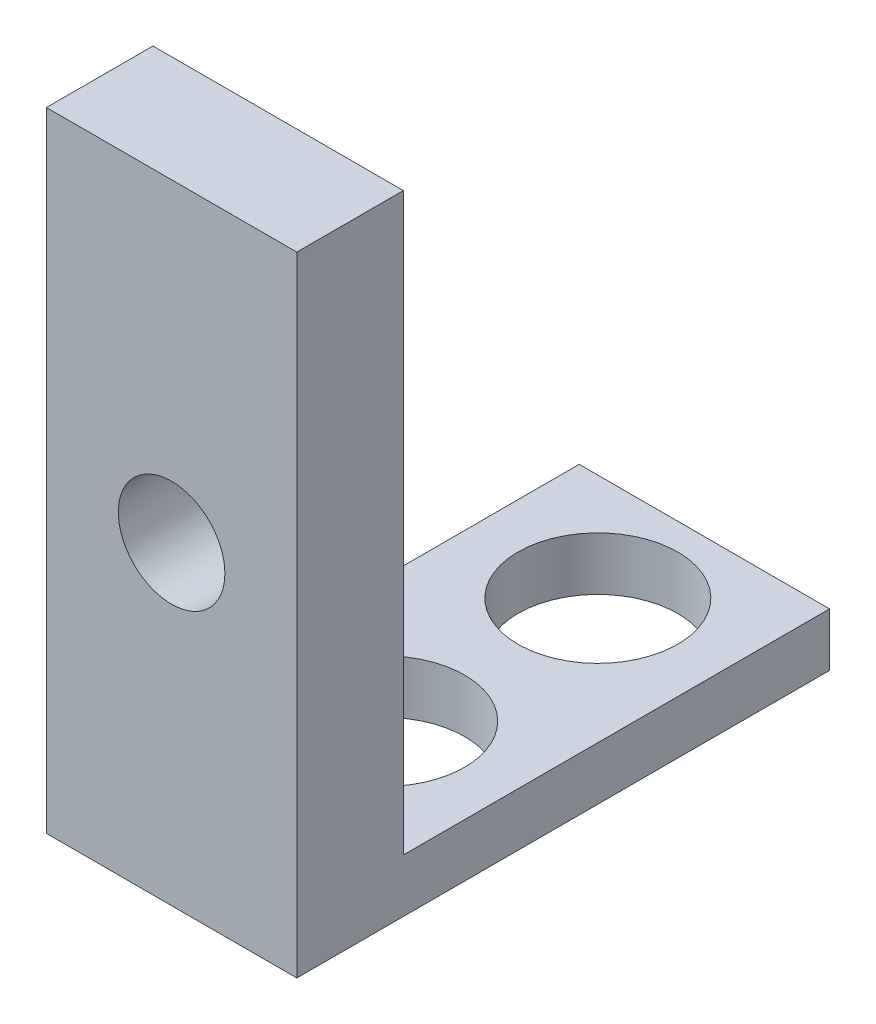
SolidWorks part; units mm, degrees
ref_plane "Front Plane" through (0, 0, 0) normal (0, 0, 1) x (1, 0, 0)
ref_plane "Top Plane" through (0, 0, 0) normal (0, 1, 0) x (1, 0, 0)
ref_plane "Right Plane" through (0, 0, 0) normal (1, 0, 0) x (0, 0, -1)
sketch "Sketch1" plane through (0, 0, 0) normal (0, 0, 1) x (1, 0, 0)
  line L0 (0, 0) -> (0, 11.8)
  line L1 (0, 0) -> (4.7, 0)
  line L2 (4.7, 0) -> (4.7, 11.8)
  line L3 (4.7, 11.8) -> (0, 11.8)
  circle A0 centre (2.35, 5.9) radius 1
  point P3 (2.35, 11.8)
  point P6 (2.35, 5.9)
  dimension "D3" = 2
  dimension "D1" = 11.8
  dimension "D2" = 4.7
extrude "Boss-Extrude1" add sketch "Sketch1" along normal blind 2
sketch "Sketch2" plane through (0, 0, 0) normal (0, 0, -1) x (-1, 0, 0)
  line L0 (0, 11.8) -> (0, 0) construction
  line L1 (-4.7, 0) -> (0, 0)
  line L2 (-4.7, 0) -> (-4.7, 1)
  line L3 (-4.7, 1) -> (0, 1)
  line L4 (0, 0) -> (0, 1)
  dimension "D1" = 1
extrude "Boss-Extrude2" add sketch "Sketch2" along normal blind 8
sketch "Sketch3" plane through (0, 1, 0) normal (0, 1, 0) x (1, 0, 0)
  line L0 (2.35, 0) -> (2.35, 8) construction
  line L1 (0, 0) -> (4.7, 0) construction
  line L2 (0, 8) -> (4.7, 8) construction
  circle A0 centre (2.35, 2) radius 1.5
  circle A1 centre (2.35, 6) radius 1.5
  point P10 (2.35, 1.9423)
  dimension "D1" = 3
  dimension "D2" = 3
  dimension "D3" = 4
  dimension "D4" = 2
extrude "Cut-Extrude1" cut sketch "Sketch3" against normal blind 8
